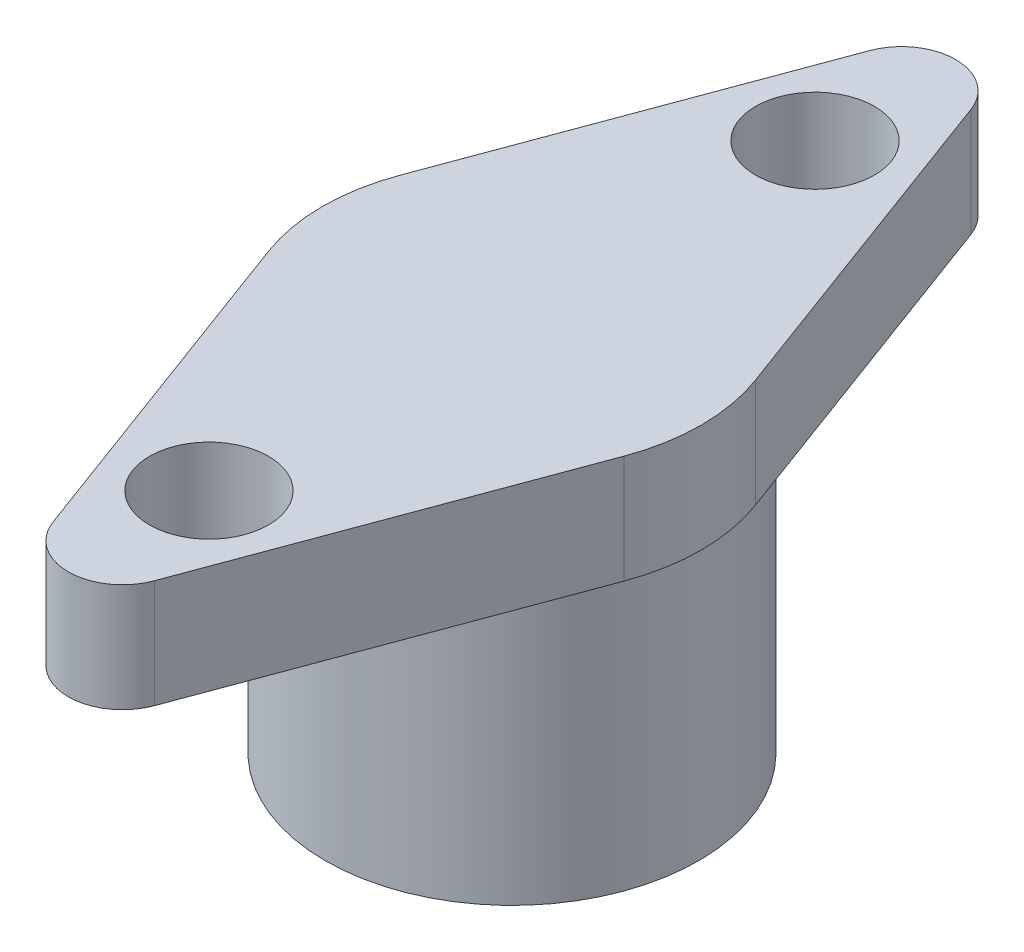
SolidWorks part; units mm, degrees
ref_plane "Front Plane" through (0, 0, 0) normal (0, 0, 1) x (1, 0, 0)
ref_plane "Top Plane" through (0, 0, 0) normal (0, 1, 0) x (1, 0, 0)
ref_plane "Right Plane" through (0, 0, 0) normal (1, 0, 0) x (0, 0, -1)
sketch "Sketch1" plane through (0, 0, 0) normal (0, 1, 0) x (1, 0, 0)
  circle A0 centre (0, 0) radius 2.1
  circle A1 centre (0, 0) radius 3.45
  dimension "D1" = 4.2
  dimension "D2" = 6.9
extrude "Boss-Extrude1" add sketch "Sketch1" along normal blind 5
sketch "Sketch2" plane through (0, 5, 0) normal (0, 1, 0) x (1, 0, 0)
  line L0 (-3.2823, 1.2152) -> (-0.9378, 7.5475)
  line L1 (0.9378, 7.5475) -> (3.2823, 1.2152)
  line L2 (3.5, 0) -> (-3.5, 0) construction
  line L3 (-3.2823, -1.2152) -> (-0.9378, -7.5475)
  line L4 (0.9378, -7.5475) -> (3.2823, -1.2152)
  line L5 (0, 7.2003) -> (0, -7.2003) construction
  arc A0 (-3.2823, 1.2152) -> (-3.2823, -1.2152) centre (0, 0) ccw
  arc A1 (-0.9378, -7.5475) -> (0.9378, -7.5475) centre (0, -7.2003) ccw
  arc A2 (-0.9378, 7.5475) -> (0.9378, 7.5475) centre (0, 7.2003) cw
  arc A3 (3.2823, -1.2152) -> (3.2823, 1.2152) centre (0, 0) ccw
  circle A6 centre (0, -5.6) radius 1.1
  circle A7 centre (0, 5.6) radius 1.1
  point P13 (0, -10.0804)
  point P16 (0, 10.0804)
  dimension "D1" = 1
  dimension "D2" = 3.5
  dimension "D4" = 5.6
  dimension "D5" = 2.2
  dimension "D3" = 7.2003
extrude "Boss-Extrude2" add sketch "Sketch2" along normal blind 2
